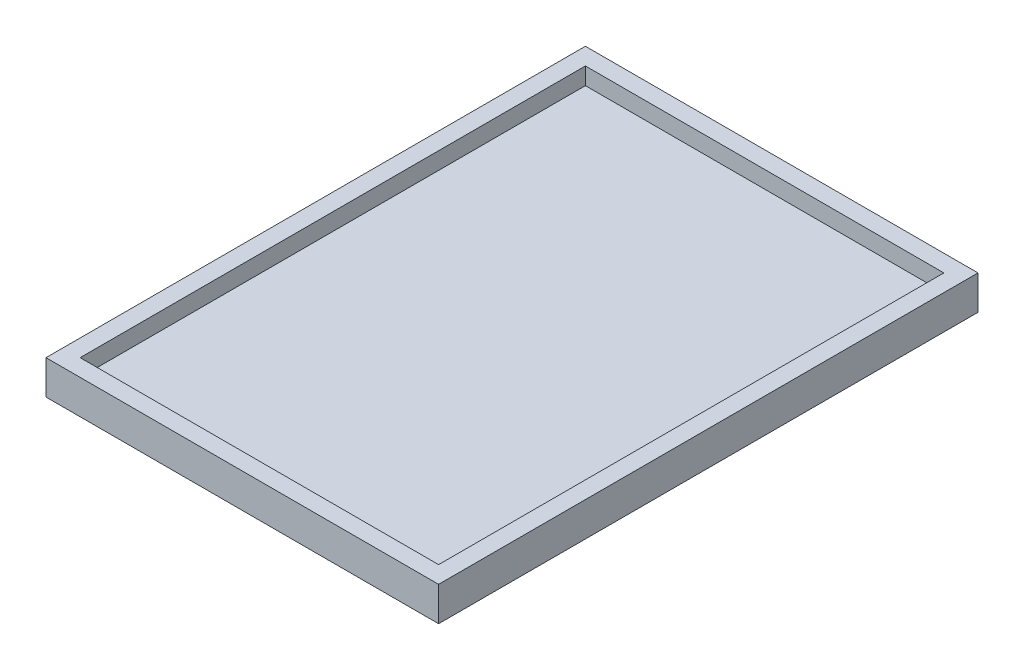
SolidWorks part; units mm, degrees
ref_plane "Alzado" through (0, 0, 0) normal (0, 0, 1) x (1, 0, 0)
ref_plane "Planta" through (0, 0, 0) normal (0, 1, 0) x (1, 0, 0)
ref_plane "Vista lateral" through (0, 0, 0) normal (1, 0, 0) x (0, 0, -1)
sketch "Croquis1" plane through (0, 0, 0) normal (0, 1, 0) x (1, 0, 0)
  line L1 (0, 0) -> (115, 0)
  line L2 (0, 0) -> (0, 158)
  line L3 (0, 158) -> (115, 158)
  line L4 (115, 0) -> (115, 158)
  dimension "D1" = 158
  dimension "D2" = 115
extrude "Saliente-Extruir1" add sketch "Croquis1" along normal blind 10
sketch "Croquis2" plane through (0, 10, 0) normal (0, 1, 0) x (1, 0, 0)
  line L0 (0, 158) -> (0, 0) construction
  line L1 (5, 153) -> (110, 153)
  line L2 (5, 153) -> (5, 5)
  line L3 (5, 5) -> (110, 5)
  line L4 (110, 153) -> (110, 5)
  line L5 (115, 0) -> (115, 158) construction
  line L6 (115, 158) -> (0, 158) construction
  line L7 (0, 0) -> (115, 0) construction
  point P8 (57.5, 158)
  dimension "D1" = 5
  dimension "D2" = 5
  dimension "D3" = 5
  dimension "D4" = 5
extrude "Cortar-Extruir2" cut sketch "Croquis2" against normal blind 5
